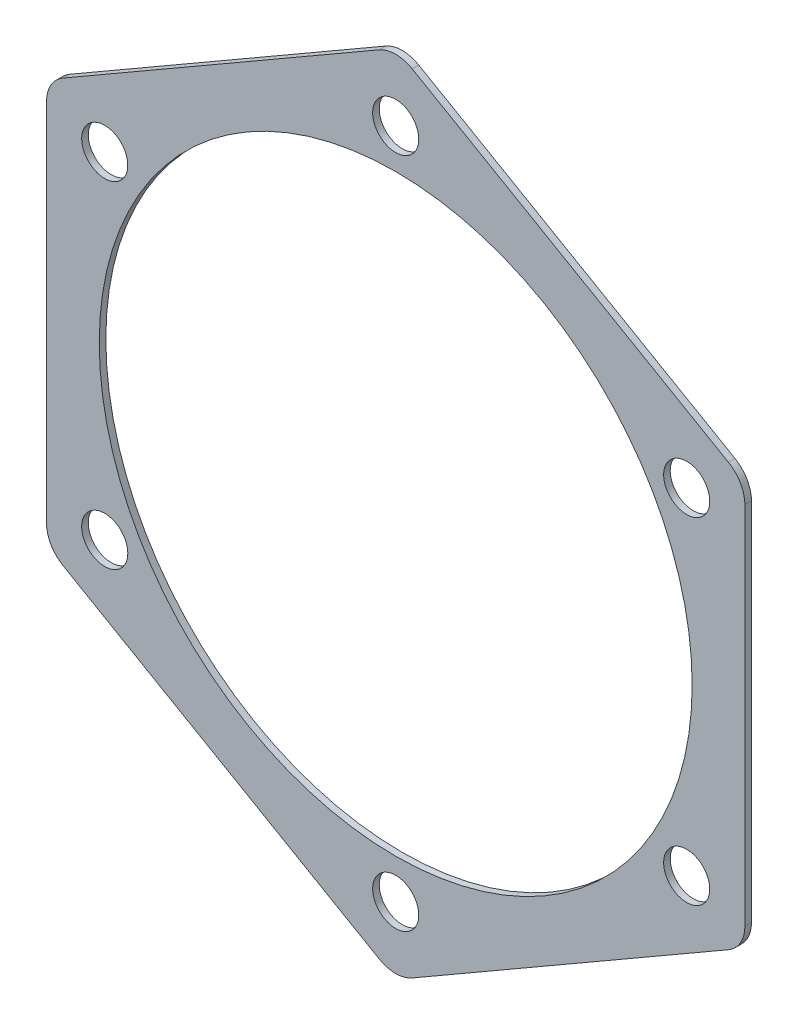
SolidWorks part; units mm, degrees
material "Rubber"
ref_plane "Front Plane" through (0, 0, 0) normal (0, 0, 1) x (1, 0, 0)
ref_plane "Top Plane" through (0, 0, 0) normal (0, 1, 0) x (1, 0, 0)
ref_plane "Right Plane" through (0, 0, 0) normal (1, 0, 0) x (0, 0, -1)
sketch "Sketch1" plane through (0, 0, 0) normal (0, 0, 1) x (1, 0, 0)
  line L1 (0, 61.1991) -> (-53, 30.5996)
  line L2 (-53, 30.5996) -> (-53, -30.5996)
  line L3 (-53, -30.5996) -> (0, -61.1991)
  line L4 (0, -61.1991) -> (53, -30.5996)
  line L5 (53, -30.5996) -> (53, 30.5996)
  line L6 (53, 30.5996) -> (0, 61.1991)
  circle A0 centre (0, 0) radius 61.1991 construction
  dimension "D1" = 106
extrude "Body" add sketch "Sketch1" along normal mid plane 1
sketch "Sketch2" plane through (0, 0, 0) normal (0, 0, 1) x (1, 0, 0)
  circle A0 centre (0, 0) radius 45
  dimension "D1" = 90
extrude "Center Hole" cut sketch "Sketch2" against normal mid plane 1
sketch "Sketch3" plane through (0, 0, 0) normal (0, 0, 1) x (1, 0, 0)
  circle A0 centre (0, 0) radius 51 construction
  circle A1 centre (0, 51) radius 3.5
  dimension "D1" = 102
  dimension "D2" = 7
extrude "Outer Holes" cut sketch "Sketch3" against normal mid plane 1
pattern_circular "CirPattern1" count 6 over 360 about axis through (0, 0, 0) along (0, 0, 1) of "Outer Holes"
fillet "R5 Fillets" radius 5 6 edges at (53, 30.5996, 0) (53, -30.5996, 0) (0, -61.1991, 0) (-53, -30.5996, 0) (-53, 30.5996, 0) (0, 61.1991, 0)
